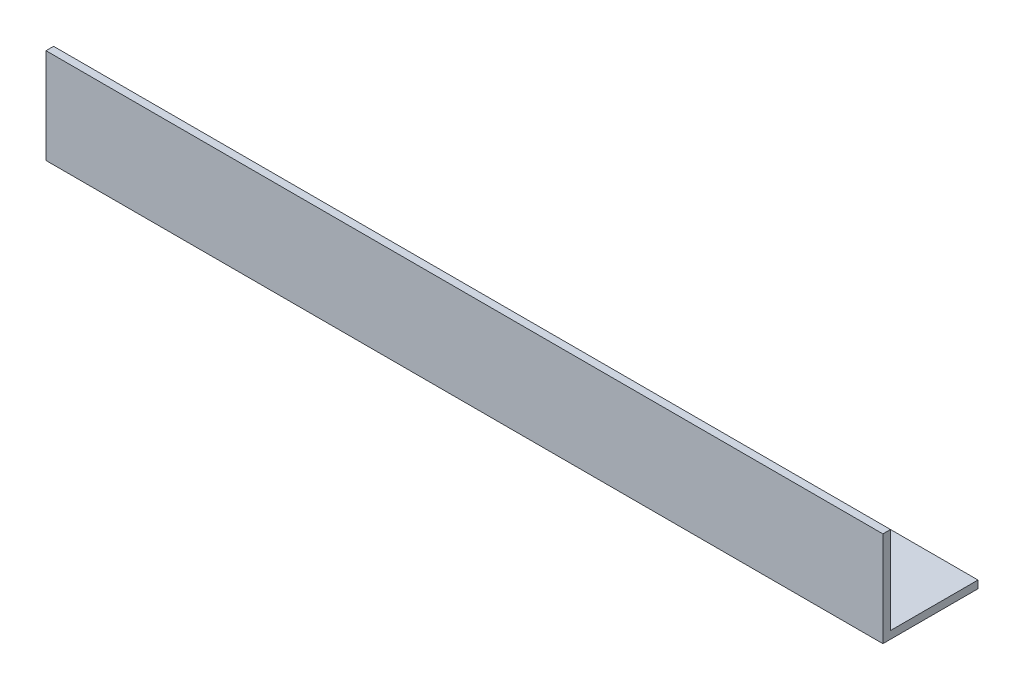
SolidWorks part; units mm, degrees
ref_plane "Спереди" through (0, 0, 0) normal (0, 0, 1) x (1, 0, 0)
ref_plane "Сверху" through (0, 0, 0) normal (0, 1, 0) x (1, 0, 0)
ref_plane "Справа" through (0, 0, 0) normal (1, 0, 0) x (0, 0, -1)
sketch "Эскиз1" plane through (0, 0, 0) normal (1, 0, 0) x (0, 0, -1)
  line L0 (0, 25) -> (0, 0)
  line L1 (0, 0) -> (25, 0)
extrude "Вытянуть-Тонкостенный1" add sketch "Эскиз1" along normal blind 220 thin thin type one direction reverse wall 2
sketch "Эскиз3" plane through (0, 0, 0) normal (0, -1, 0) x (1, 0, 0)
  line L0 (0, -25) -> (14.445, -18.1903)
  line L1 (14.445, -18.1903) -> (31.8984, -25)
  line L2 (220, -25) -> (0, -25) construction
  line L3 (0, -25) -> (31.8984, -25)
  line L4 (40, -25) -> (54.445, -18.1903)
  line L5 (54.445, -18.1903) -> (71.8984, -25)
  line L6 (40, -25) -> (71.8984, -25)
  line L7 (80, -25) -> (94.445, -18.1903)
  line L8 (94.445, -18.1903) -> (111.8984, -25)
  line L9 (80, -25) -> (111.8984, -25)
  line L10 (120, -25) -> (134.445, -18.1903)
  line L11 (134.445, -18.1903) -> (151.8984, -25)
  line L12 (120, -25) -> (151.8984, -25)
  line L13 (160, -25) -> (174.445, -18.1903)
  line L14 (174.445, -18.1903) -> (191.8984, -25)
  line L15 (160, -25) -> (191.8984, -25)
  dimension "D1" = 5
extrude "Вырез-Вытянуть1" cut sketch "Эскиз3" against normal through all
